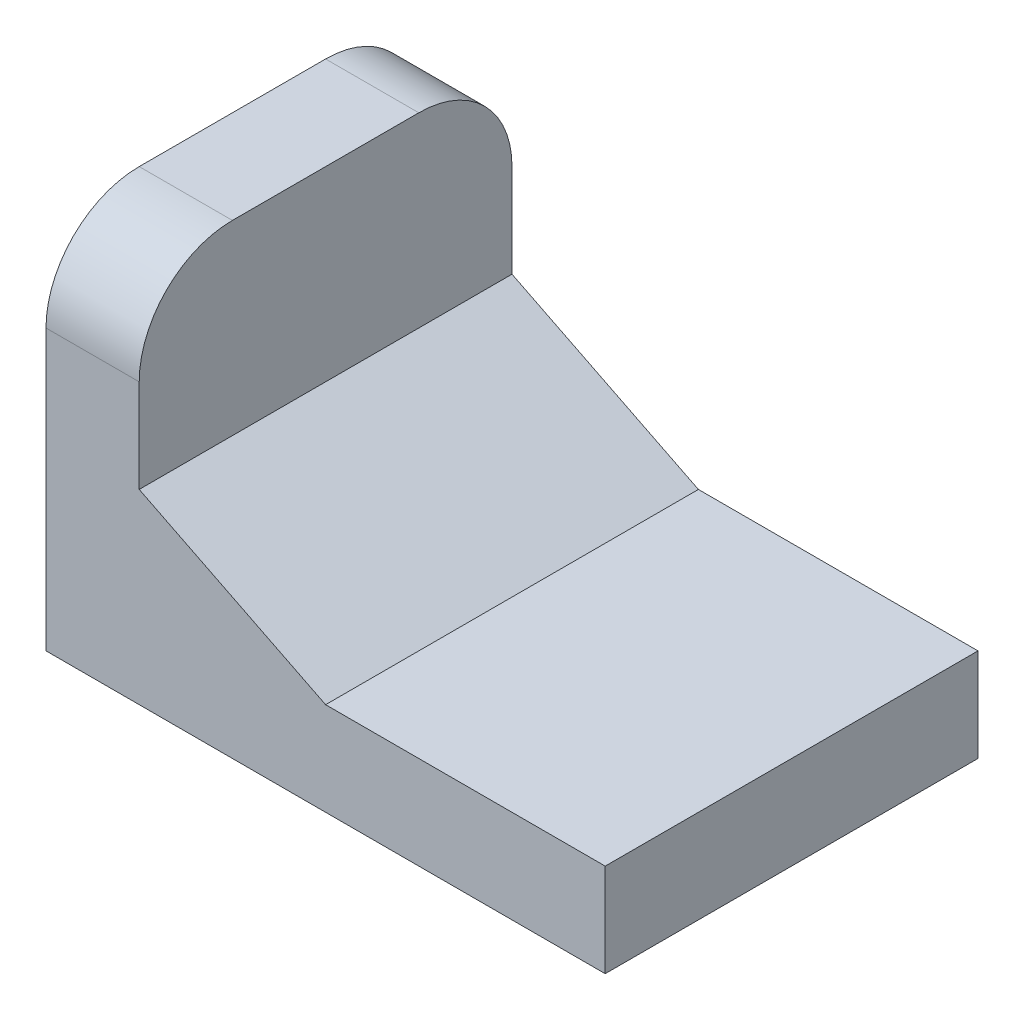
SolidWorks part; units mm, degrees
ref_plane "前基準面" through (0, 0, 0) normal (0, 0, 1) x (1, 0, 0)
ref_plane "上基準面" through (0, 0, 0) normal (0, 1, 0) x (1, 0, 0)
ref_plane "右基準面" through (0, 0, 0) normal (1, 0, 0) x (0, 0, -1)
sketch "草圖1" plane through (0, 0, 0) normal (0, 0, 1) x (1, 0, 0)
  line L0 (15, 5) -> (5, 10)
  line L1 (0, 0) -> (5, 0)
  line L2 (0, 0) -> (0, 20)
  line L3 (0, 20) -> (5, 20)
  line L4 (5, 10) -> (5, 20)
  line L5 (0, 0) -> (30, 0)
  line L6 (0, 0) -> (0, 5)
  line L7 (15, 5) -> (30, 5)
  line L8 (30, 0) -> (30, 5)
  point P10 (2.5, 20)
  dimension "D1" = 30
  dimension "D2" = 5
  dimension "D3" = 15
  dimension "D4" = 20
  dimension "D5" = 5
  dimension "D6" = 10
extrude "填料-伸長1" add sketch "草圖1" along normal blind 20 contours L5 L8 L7 L0 L4 L3 L2 L1
fillet "圓角1" radius 5 2 edges at (2.5, 20, 0) (2.5, 20, 20)
